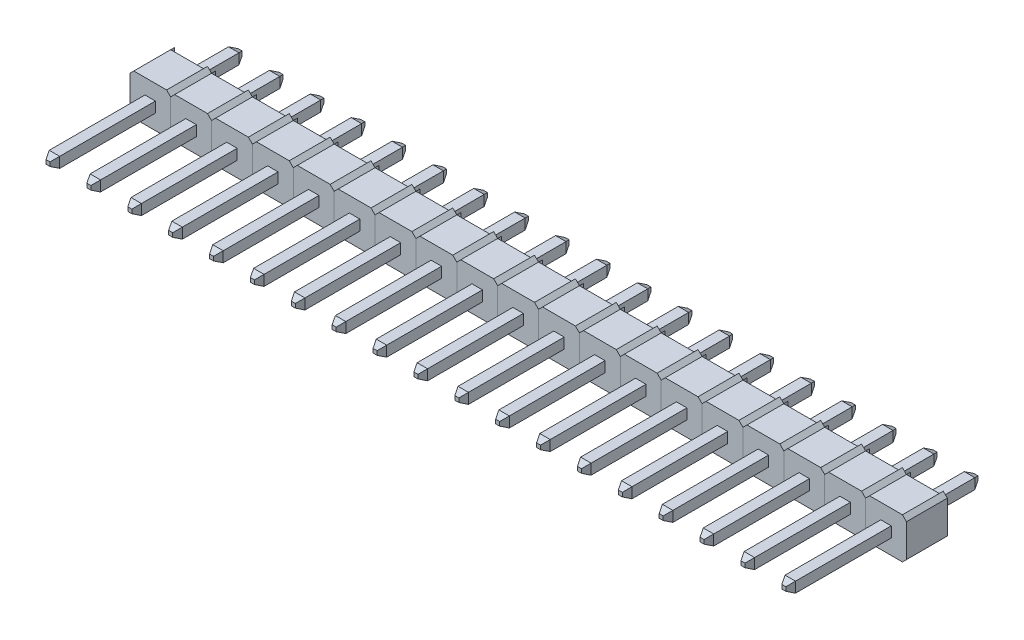
SolidWorks part; units mm, degrees
other "Бобышка-Штырь"
ref_plane "Front Plane" through (0, 0, 0) normal (0, 0, 1) x (1, 0, 0)
ref_plane "Top Plane" through (0, 0, 0) normal (0, 1, 0) x (1, 0, 0)
ref_plane "Right Plane" through (0, 0, 0) normal (1, 0, 0) x (0, 0, -1)
sketch "Эскиз-Сечение-Пина" plane through (0, 0, 0) normal (0, 0, 1) x (1, 0, 0)
  line L0 (1.02, 1.27) -> (1.27, 1.02)
  line L1 (-1.02, 1.27) -> (1.02, 1.27)
  line L2 (-1.27, 1.02) -> (-1.27, -1.02)
  line L3 (-1.02, -1.27) -> (1.02, -1.27)
  line L4 (1.27, 1.02) -> (1.27, -1.02)
  line L5 (-1.145, 1.145) -> (1.145, -1.145) construction
  line L6 (-1.145, -1.145) -> (1.145, 1.145) construction
  line L12 (-0.325, -0.325) -> (0.325, -0.325)
  line L13 (-1.27, -1.02) -> (-1.02, -1.27)
  line L14 (-1.27, 1.02) -> (-1.02, 1.27)
  line L15 (1.02, -1.27) -> (1.27, -1.02)
  line L16 (-0.325, -0.325) -> (-0.325, 0.325)
  line L17 (-0.325, 0.325) -> (0.325, 0.325)
  line L18 (0.325, -0.325) -> (0.325, 0.325)
  line L19 (-0.325, -0.325) -> (0.325, 0.325) construction
  line L20 (-0.325, 0.325) -> (0.325, -0.325) construction
  point P0 (0, 0)
  point P1 (0, 0)
  dimension "D1" = 2.54
  dimension "D2" = 0.25
  dimension "D3" = 0.65
extrude "Бобышка-Пластик-Основной" add sketch "Эскиз-Сечение-Пина" along normal blind 2.29
sketch "Эскиз-Пластик-Проставки" plane through (0, 0, 0) normal (0, 0, -1) x (-1, 0, 0)
  line L0 (-1.02, 1.27) -> (-1.27, 1.02)
  line L1 (-1.27, 1.02) -> (-1.27, -1.02)
  line L2 (-1.27, -1.02) -> (-1.02, -1.27)
  line L3 (-1.02, -1.27) -> (-1.02, 1.27)
  line L4 (1.02, 1.27) -> (1.27, 1.02)
  line L5 (1.27, 1.02) -> (1.27, -1.02)
  line L6 (1.27, -1.02) -> (1.02, -1.27)
  line L7 (1.02, -1.27) -> (1.02, 1.27)
extrude "Бобышка-Пластик-Проставки" add sketch "Эскиз-Пластик-Проставки" along normal blind 0.25
sketch "Эскиз-Штырь" plane through (0, 0, 2.29) normal (0, 0, 1) x (1, 0, 0)
  line L1 (-0.325, 0.325) -> (0.325, 0.325)
  line L2 (-0.325, 0.325) -> (-0.325, -0.325)
  line L3 (-0.325, -0.325) -> (0.325, -0.325)
  line L4 (0.325, 0.325) -> (0.325, -0.325)
  line L5 (-0.325, 0.325) -> (0.325, -0.325) construction
  line L6 (-0.325, -0.325) -> (0.325, 0.325) construction
  point P4 (0, 0)
extrude "Бобышка-Штырь" add sketch "Эскиз-Штырь" along normal blind 6.35 and the other way offset from surface (5.59 mm away) 3.3 from surface at 0 separate body other way up to face at (0, 0, 0) starting at face at (0, 0, 2.29)
chamfer "Фаска-Штыря-Верхняя" distance 0.2 angle 63.435 4 edges at (0, -0.325, 8.64) (-0.325, 0, 8.64) (0, 0.325, 8.64) (0.325, 0, 8.64)
chamfer "Фаска-Штыря-Нижняя" distance 0.2 angle 63.435 4 edges at (-0.325, 0, -3.3) (0, 0.325, -3.3) (0.325, 0, -3.3) (0, -0.325, -3.3)
pattern_linear "Линейный-массив" count 19 spacing 2.54 along (-1, 0, 0) of bodies 103 104
